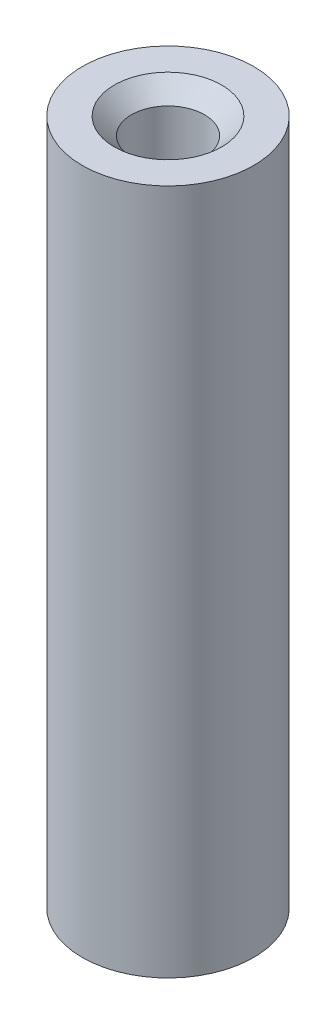
SolidWorks part; units mm, degrees
ref_plane "Front Plane" through (0, 0, 0) normal (0, 0, 1) x (1, 0, 0)
ref_plane "Top Plane" through (0, 0, 0) normal (0, 1, 0) x (1, 0, 0)
ref_plane "Right Plane" through (0, 0, 0) normal (1, 0, 0) x (0, 0, -1)
sketch "Sketch1" plane through (0, 0, 0) normal (0, 1, 0) x (1, 0, 0)
  circle A0 centre (0, 0) radius 3.175
  dimension "D1" = 6.35
extrude "Boss-Extrude1" add sketch "Sketch1" along normal blind 25.4
hole_wizard "#6-32 Tapped Hole1" positions "Sketch4" profile "Sketch3" tap size "#6-32" standard "ANSI Inch" end condition through all
sketch "Sketch4" plane through (0, 25.4, 0) normal (0, 1, 0) x (-1, 0, 0)
  point P0 (0, 0)
sketch "Sketch3" plane through (0, 25.4, 0) normal (1, 0, 0) x (0, 0, 1)
  line L0 (0, 0) -> (0, 25.4)
  line L1 (0, 25.4) -> (1.9875, 25.4)
  line L2 (1.3525, 24.765) -> (1.3525, 0.635)
  line L3 (1.3525, 0.635) -> (1.9875, 0)
  line L5 (1.9875, 0) -> (0, 0)
  line L6 (-1.3525, 0.635) -> (-1.9875, 0) construction
  line L7 (1.9875, 25.4) -> (1.3525, 24.765)
  line L8 (-1.9876, 25.4) -> (-1.3526, 24.765) construction
  line L11 (0, -6.35) -> (0, 107.95) construction
  dimension "Thread Major Dia." = 2.7051
  dimension "Thru Tap Drill Depth" = 25.4
  dimension "Near C'Sink Dia." = 3.9751
  dimension "Near C'Sink Angle" = 90
  dimension "Far C'Sink Dia." = 3.9751
  dimension "Far C'Sink Angle" = 90
